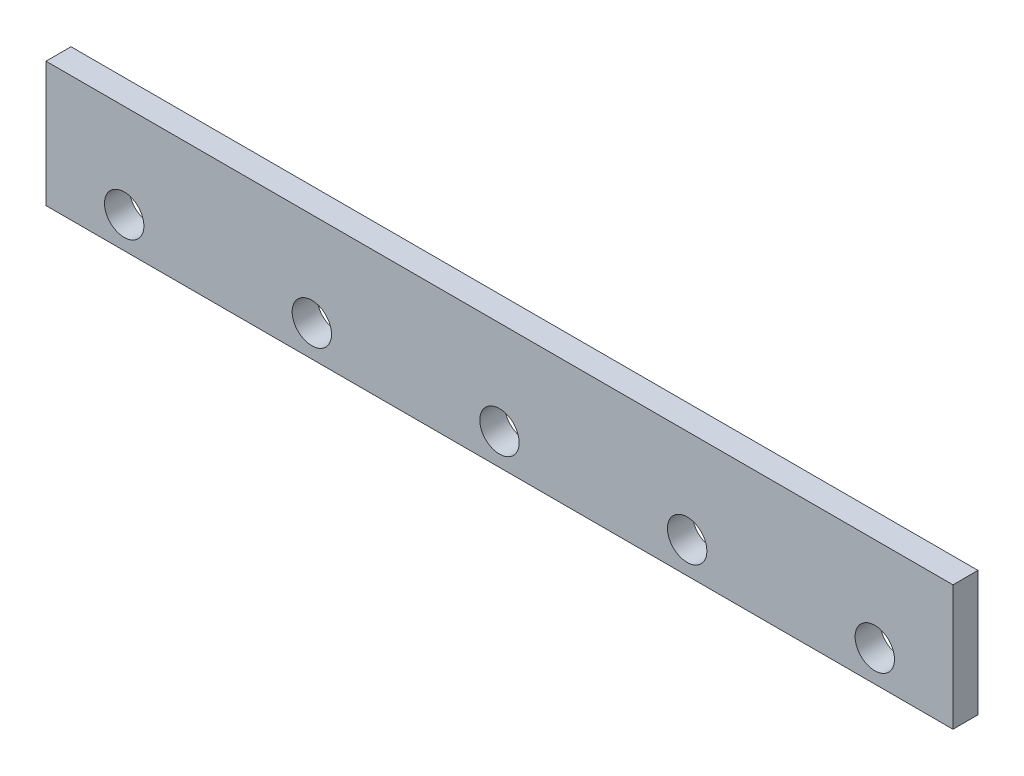
SolidWorks part; units mm, degrees
ref_plane "Front Plane" through (0, 0, 0) normal (0, 0, 1) x (1, 0, 0)
ref_plane "Top Plane" through (0, 0, 0) normal (0, 1, 0) x (1, 0, 0)
ref_plane "Right Plane" through (0, 0, 0) normal (1, 0, 0) x (0, 0, -1)
sketch "Sketch1" plane through (0, 0, 0) normal (0, 0, 1) x (1, 0, 0)
  line L1 (0, 0) -> (580, 0)
  line L2 (0, 0) -> (0, 80)
  line L3 (0, 80) -> (580, 80)
  line L4 (580, 0) -> (580, 80)
  circle A0 centre (50, 20) radius 12.6
  circle A1 centre (170, 20) radius 12.6
  circle A2 centre (290, 20) radius 12.6
  circle A3 centre (410, 20) radius 12.6
  circle A4 centre (530, 20) radius 12.6
  dimension "D3" = 25.2
  dimension "D4" = 50
  dimension "D1" = 580
  dimension "D2" = 80
  dimension "D5" = 60
  dimension "D6" = 120
  dimension "D7" = 120
  dimension "D8" = 120
  dimension "D9" = 120
extrude "Boss-Extrude1" add sketch "Sketch1" along normal blind 16
